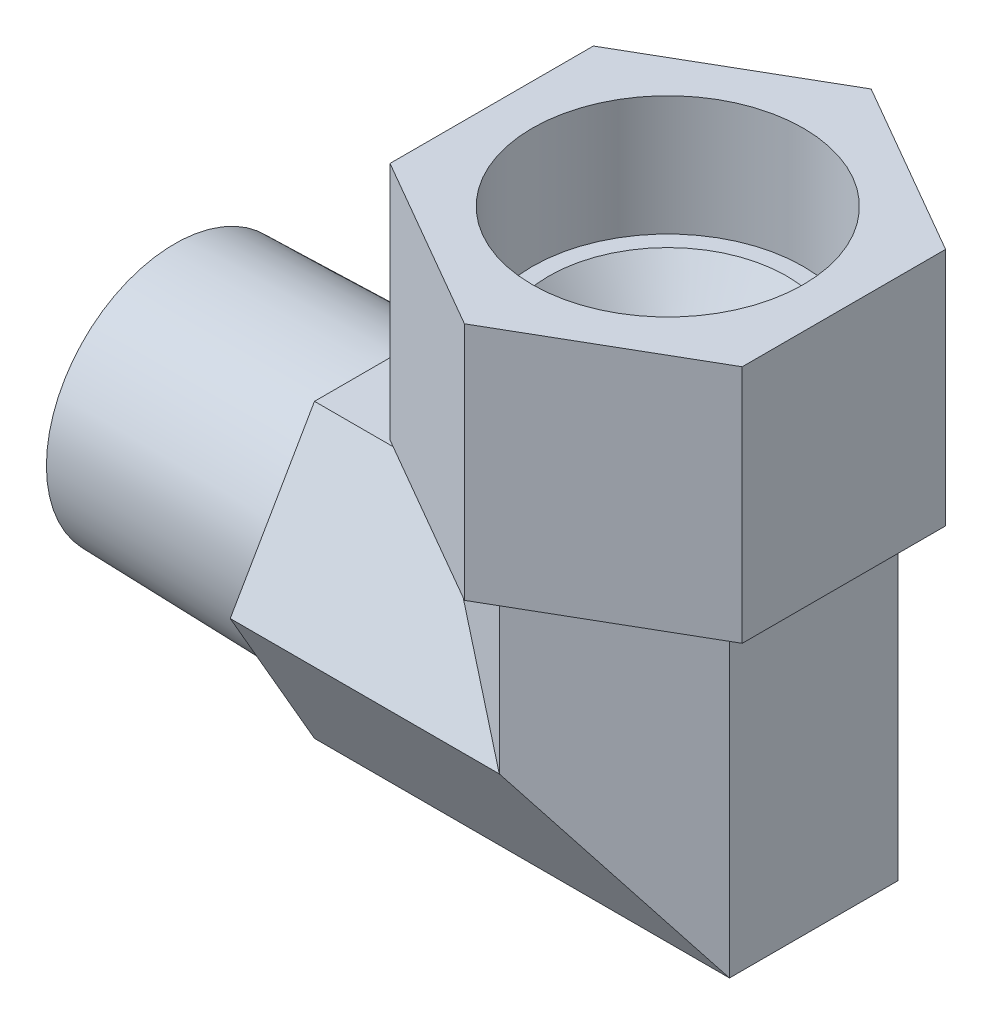
SolidWorks part; units mm, degrees
material "2024-T3"
ref_plane "Front Plane" through (0, 0, 0) normal (0, 0, 1) x (1, 0, 0)
ref_plane "Top Plane" through (0, 0, 0) normal (0, 1, 0) x (1, 0, 0)
ref_plane "Right Plane" through (0, 0, 0) normal (1, 0, 0) x (0, 0, -1)
sketch "Sketch1" plane through (0, 0, 0) normal (0, 0, 1) x (1, 0, 0)
  line L0 (0, 0) -> (33.9096, 0) construction
  line L7 (0, 0) -> (44.45, 0)
  line L8 (44.45, 0) -> (44.45, 25.908)
  dimension "D1" = 44.45
  dimension "D2" = 25.908
ref_plane "Plane1" through (0, 0, 0) normal (1, 0, 0) x (0, 0, -1)
sketch "Sketch2" plane through (0, 0, 0) normal (1, 0, 0) x (0, 0, -1)
  line L0 (0, 0) -> (27.4531, 0) construction
  line L1 (7.5963, 13.1572) -> (-7.5963, 13.1572)
  line L2 (-7.5963, 13.1572) -> (-15.1926, 0)
  line L3 (-15.1926, 0) -> (-7.5963, -13.1572)
  line L4 (-7.5963, -13.1572) -> (7.5963, -13.1572)
  line L5 (7.5963, -13.1572) -> (15.1926, 0)
  line L6 (15.1926, 0) -> (7.5963, 13.1572)
  circle A0 centre (0, 0) radius 13.1572 construction
  dimension "D1" = 26.3144
sweep "Sweep1" add profiles "Sketch2" path "Sketch1"
sketch "Sketch3" plane through (0, 0, 0) normal (-1, 0, 0) x (0, 0, 1)
  circle A0 centre (0, 0) radius 9.1313
  dimension "D1" = 18.2626
extrude "Cut-Extrude1" cut sketch "Sketch3" against normal blind 52.1843
sketch "Sketch4" plane through (0, 25.908, 0) normal (0, 1, 0) x (1, 0, 0)
  line L0 (0, 0) -> (44.45, 0) construction
  line L1 (44.45, 15.1926) -> (44.45, -15.1926) construction
  line L2 (44.45, -15.1926) -> (31.2928, -7.5963) construction
  line L3 (0, -15.1926) -> (44.45, -15.1926) construction
  line L4 (57.6072, 0) -> (31.2928, 0) construction
  line L5 (57.6072, -7.5963) -> (57.6072, 7.5963) construction
  line L6 (31.2928, 7.5963) -> (31.2928, -7.5963) construction
  circle A0 centre (44.45, 0) radius 7.7343
  dimension "D1" = 15.4686
extrude "Cut-Extrude2" cut sketch "Sketch4" against normal blind 25.908
chamfer "Chamfer1" distance 3.9624 angle 37 1 edges at (36.7157, 25.908, 0)
sketch "Sketch5" plane through (0, 0, 0) normal (-1, 0, 0) x (0, 0, 1)
  line L6 (-7.5963, 13.1572) -> (-15.1926, 0)
  line L7 (-15.1926, 0) -> (-7.5963, -13.1572)
  line L8 (-7.5963, -13.1572) -> (7.5963, -13.1572)
  line L9 (7.5963, -13.1572) -> (15.1926, 0)
  line L10 (15.1926, 0) -> (7.5963, 13.1572)
  line L11 (7.5963, 13.1572) -> (-7.5963, 13.1572)
  line L12 (-7.5963, 13.1572) -> (-15.1926, 0)
  line L13 (-15.1926, 0) -> (-7.5963, -13.1572)
  line L14 (-7.5963, -13.1572) -> (7.5963, -13.1572)
  line L15 (7.5963, -13.1572) -> (15.1926, 0)
  line L16 (15.1926, 0) -> (7.5963, 13.1572)
  line L17 (7.5963, 13.1572) -> (-7.5963, 13.1572)
  circle A0 centre (0, 0) radius 11.5633
  dimension "D2" = 23.1267
  dimension "D1" = 0
extrude "Cut-Extrude3" cut sketch "Sketch5" against normal blind 20.1981 draft 1.47
sketch "Sketch6" plane through (0, 0, 0) normal (-1, 0, 0) x (0, 0, 1)
  line L0 (-15.1926, 0) -> (-7.5963, 13.1572) construction
  line L1 (-15.1926, 0) -> (-7.5963, 13.1572)
  line L2 (-7.5963, 13.1572) -> (7.5963, 13.1572) construction
  line L3 (-7.5963, 13.1572) -> (7.5963, 13.1572)
  line L4 (7.5963, 13.1572) -> (15.1926, 0) construction
  line L5 (7.5963, 13.1572) -> (15.1926, 0)
  line L6 (15.1926, 0) -> (7.5963, -13.1572) construction
  line L7 (15.1926, 0) -> (7.5963, -13.1572)
  line L8 (7.5963, -13.1572) -> (-7.5963, -13.1572) construction
  line L9 (7.5963, -13.1572) -> (-7.5963, -13.1572)
  line L10 (-7.5963, -13.1572) -> (-15.1926, 0) construction
  line L11 (-7.5963, -13.1572) -> (-15.1926, 0)
  circle A0 centre (0, 0) radius 12.0817 construction
  circle A1 centre (0, 0) radius 12.0817
extrude "Cut-Extrude4" cut sketch "Sketch6" against normal up to surface (20.1981 mm away) up to face at (20.1981, 0, 12.0817)
sketch "Sketch7" plane through (0, 25.908, 0) normal (0, 1, 0) x (1, 0, 0)
  line L0 (57.6072, 7.5963) -> (57.6072, -7.5963) construction
  line L1 (44.45, 18.3309) -> (28.575, 9.1654)
  line L2 (28.575, 9.1654) -> (28.575, -9.1654)
  line L3 (28.575, -9.1654) -> (44.45, -18.3309)
  line L4 (44.45, -18.3309) -> (60.325, -9.1654)
  line L5 (60.325, -9.1654) -> (60.325, 9.1654)
  line L6 (60.325, 9.1654) -> (44.45, 18.3309)
  circle A0 centre (44.45, 0) radius 15.875 construction
  circle A1 centre (44.45, 0) radius 12.2174
  dimension "D2" = 24.4348
  dimension "D1" = 31.75
extrude "Boss-Extrude1" add sketch "Sketch7" along normal mid plane 21.59
